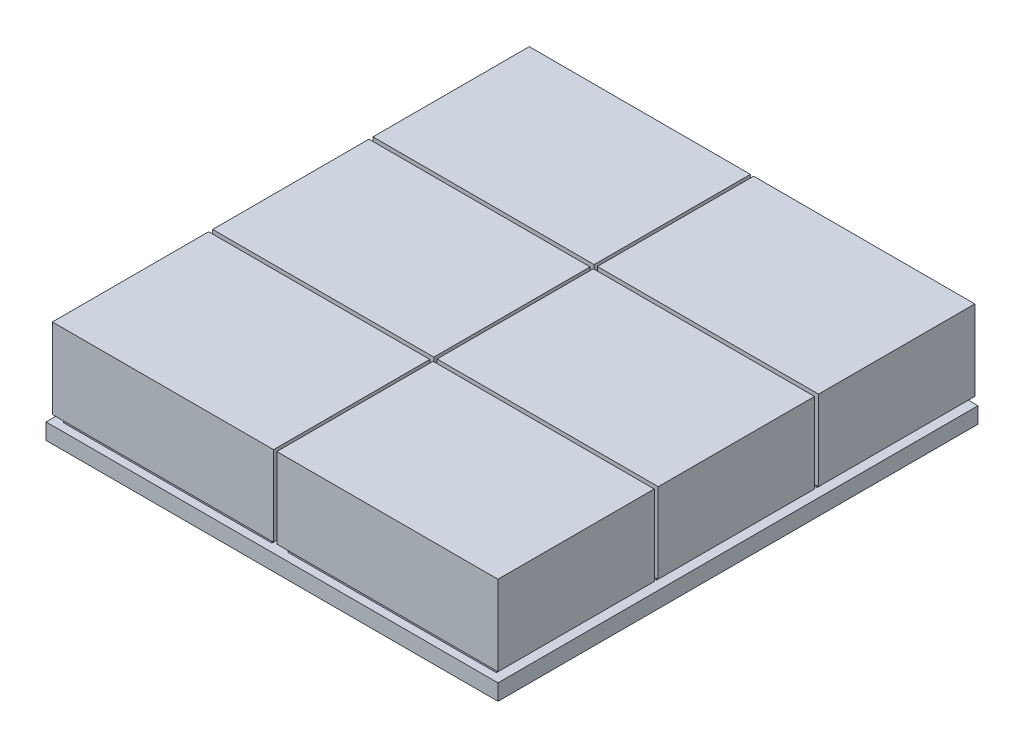
SolidWorks part; units mm, degrees
ref_plane "Front Plane" through (0, 0, 0) normal (0, 0, 1) x (1, 0, 0)
ref_plane "Top Plane" through (0, 0, 0) normal (0, 1, 0) x (1, 0, 0)
ref_plane "Right Plane" through (0, 0, 0) normal (1, 0, 0) x (0, 0, -1)
sketch "Sketch1" plane through (0, 0, 0) normal (0, 1, 0) x (1, 0, 0)
  line L1 (-35.5, -125) -> (35.5, -125)
  line L2 (-35.5, -125) -> (-35.5, 125)
  line L3 (-35.5, 125) -> (35.5, 125)
  line L4 (35.5, -125) -> (35.5, 125)
  line L5 (-35.5, -125) -> (35.5, 125) construction
  line L6 (-35.5, 125) -> (35.5, -125) construction
  point P0 (0, 0)
  dimension "D1" = 71
  dimension "D2" = 250
extrude "Boss-Extrude1" add sketch "Sketch1" along normal blind 5
sketch "Sketch2" plane through (0, 5, 0) normal (0, 1, 0) x (1, 0, 0)
  line L0 (0, 0) -> (0, -125) construction
  line L1 (-35.5, -125) -> (35.5, -125) construction
  line L3 (-32.5, -77.5) -> (32.5, -77.5)
  line L4 (-32.5, -77.5) -> (-32.5, -122.5)
  line L5 (-32.5, -122.5) -> (32.5, -122.5)
  line L6 (32.5, -77.5) -> (32.5, -122.5)
  line L7 (-32.5, -77.5) -> (32.5, -122.5) construction
  line L8 (-32.5, -122.5) -> (32.5, -77.5) construction
  point P5 (0, -100)
  dimension "D1" = 65
  dimension "D2" = 45
  dimension "D3" = 2.5
extrude "Boss-Extrude3" add sketch "Sketch2" along normal blind 2
pattern_linear "LPattern1" count 3 spacing 50 along (0, 0, -1) of "Boss-Extrude3"
sketch "Sketch3" plane through (0, 7, 0) normal (0, 1, 0) x (1, 0, 0)
  line L0 (0, 0) -> (0, -122.5) construction
  line L1 (-32.5, -122.5) -> (32.5, -122.5) construction
  line L2 (-35.5, 125) -> (-35.5, -125) construction
  line L3 (-34.5, -75.2576) -> (34.5, -75.2576)
  line L4 (-34.5, -75.2576) -> (-34.5, -124.0124)
  line L5 (-34.5, -124.0124) -> (34.5, -124.0124)
  line L6 (34.5, -75.2576) -> (34.5, -124.0124)
  line L7 (-34.5, -75.2576) -> (34.5, -124.0124) construction
  line L8 (-34.5, -124.0124) -> (34.5, -75.2576) construction
  point P5 (0, -99.635)
  dimension "D1" = 1
extrude "Boss-Extrude8" add sketch "Sketch3" along normal blind 25
pattern_linear "LPattern5" count 3 spacing 50 along (0, 0, -1) of "Boss-Extrude8"
sketch "Sketch5" plane through (0, 0, 0) normal (0, 1, 0) x (1, 0, 0)
  line L0 (0, 0) -> (208.2024, 0) construction
pattern_linear "LPattern6" count 2 spacing 70 along (1, 0, 0) of "Boss-Extrude1", "Boss-Extrude3", "LPattern1", "Boss-Extrude8", "LPattern5"
sketch "Sketch6" plane through (0, 5, 0) normal (0, 1, 0) x (1, 0, 0)
  line L0 (105.5, -125) -> (105.5, 125) construction
  line L1 (-35.5, 125) -> (105.5, 125)
  line L2 (-35.5, 125) -> (-35.5, 24.7332)
  line L3 (-35.5, 24.7332) -> (105.5, 24.7332)
  line L4 (105.5, 125) -> (105.5, 24.7332)
extrude "Cut-Extrude1" cut sketch "Sketch6" against normal blind 10
